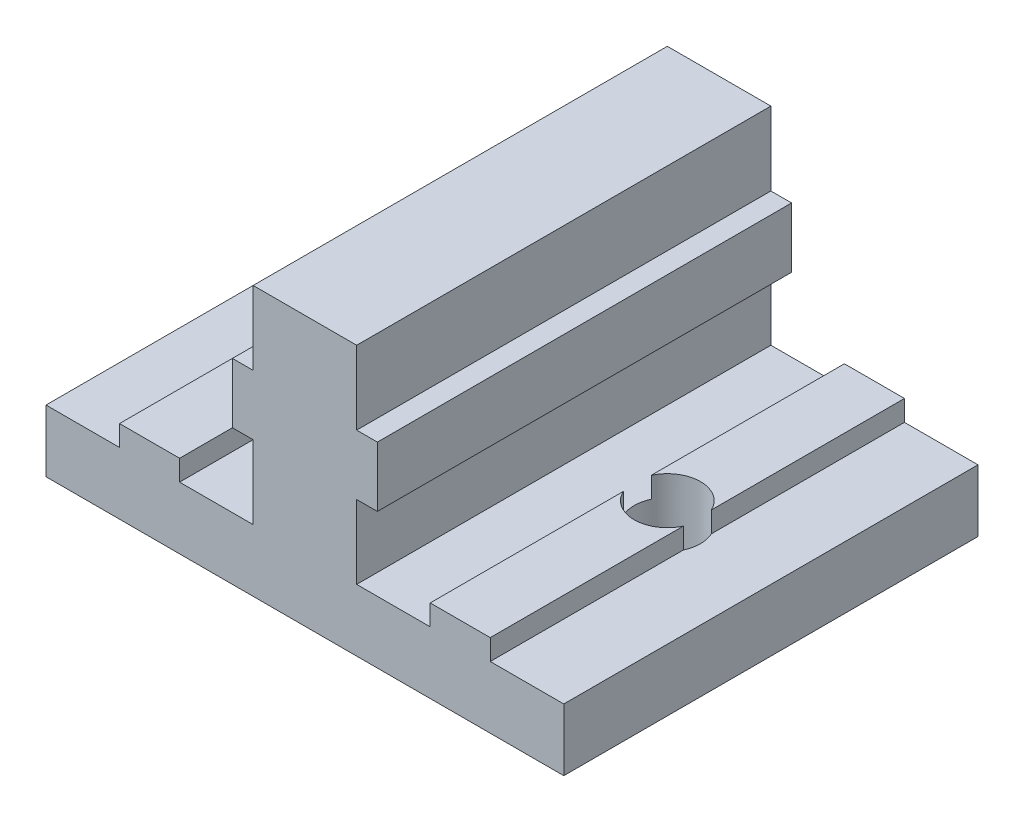
SolidWorks part; units mm, degrees
ref_plane "Front Plane" through (0, 0, 0) normal (0, 0, 1) x (1, 0, 0)
ref_plane "Top Plane" through (0, 0, 0) normal (0, 1, 0) x (1, 0, 0)
ref_plane "Right Plane" through (0, 0, 0) normal (1, 0, 0) x (0, 0, -1)
sketch "Esquisse1" plane through (0, 0, 0) normal (0, 0, 1) x (1, 0, 0)
  line L0 (-12.5, 0) -> (-12.5, 3)
  line L1 (-12.5, 3) -> (-8.95, 3)
  line L2 (-8.95, 3) -> (-8.95, 4)
  line L3 (-8.95, 4) -> (-6.05, 4)
  line L4 (-6.05, 4) -> (-6.05, 3)
  line L5 (-6.05, 3) -> (-2.5, 3)
  line L6 (-2.5, 3) -> (-2.5, 6.55)
  line L7 (0, 0) -> (-12.5, 0)
  line L8 (-2.5, 6.55) -> (-3.5, 6.55)
  line L9 (-3.5, 6.55) -> (-3.5, 9.45)
  line L10 (-3.5, 9.45) -> (-2.5, 9.45)
  line L11 (-2.5, 9.45) -> (-2.5, 13)
  line L12 (-2.5, 13) -> (0, 13)
  line L13 (0, 13) -> (0, 0)
  dimension "D1" = 10
  dimension "D2" = 3
  dimension "D3" = 1
  dimension "D4" = 2.9
  dimension "D5" = 3.55
  dimension "D6" = 2.5
  dimension "D7" = 10
  dimension "D8" = 2.9
  dimension "D9" = 3.55
extrude "Main" add sketch "Esquisse1" along normal blind 20
mirror "Symétrie1" about plane through (0, 0, 0) normal (1, 0, 0) of "Main"
sketch "Sketch1" plane through (0, 0, 0) normal (0, -1, 0) x (1, 0, 0)
  line L0 (-12.5, 0) -> (12.5, 0) construction
  line L2 (-12.5, 20) -> (-12.5, 0) construction
  line L3 (12.5, 20) -> (12.5, 0) construction
  circle A0 centre (-7.5, 10) radius 1.6
  circle A1 centre (7.5, 10) radius 1.6
  point P4 (0, 0)
  point P9 (-15, 10.7114)
  dimension "D1" = 3.2
  dimension "D2" = 10
  dimension "D3" = 5
  dimension "D4" = 5
extrude "Cut-Extrude1" cut sketch "Sketch1" against normal through all
